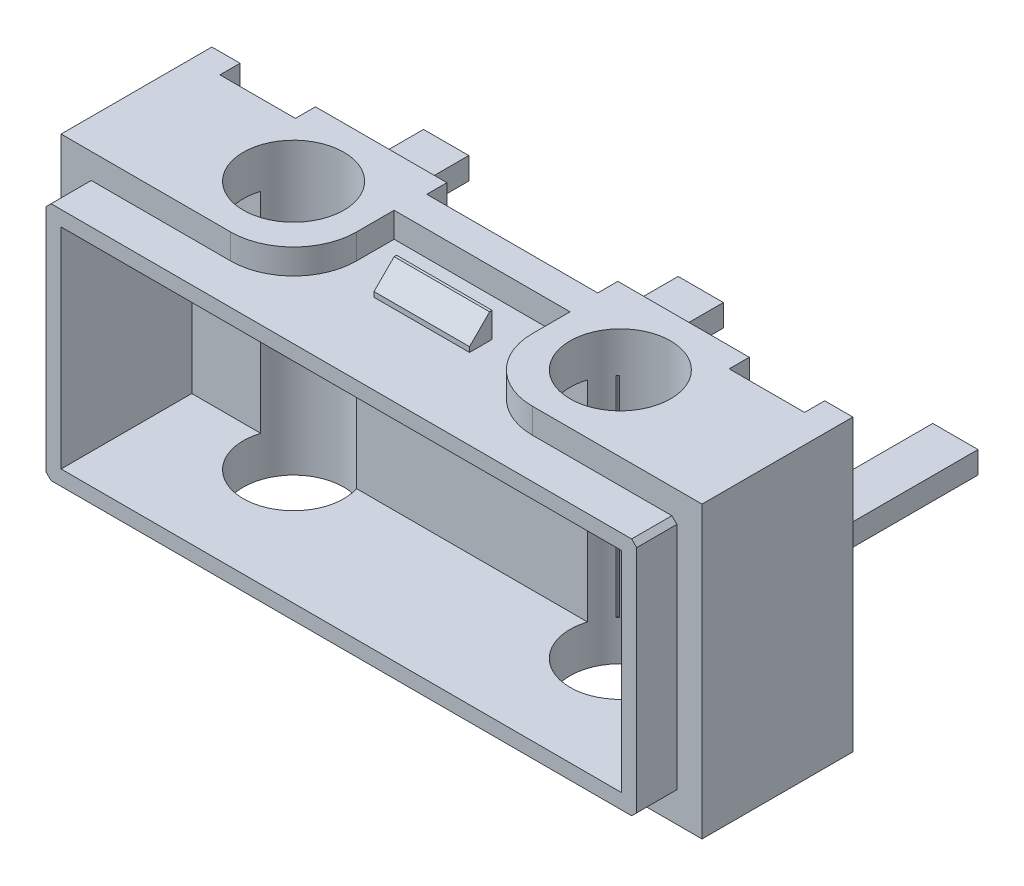
SolidWorks part; units mm, degrees
ref_plane "Face" through (0, 0, 0) normal (0, 0, 1) x (1, 0, 0)
ref_plane "Dessus" through (0, 0, 0) normal (0, 1, 0) x (1, 0, 0)
ref_plane "Droite" through (0, 0, 0) normal (1, 0, 0) x (0, 0, -1)
sketch "Esquisse1" plane through (0, 0, 0) normal (0, 0, 1) x (1, 0, 0)
  line L0 (-6.375, 0) -> (6.375, 0) construction
  line L1 (-6.375, 2.885) -> (6.375, 2.885)
  line L2 (-6.375, 2.885) -> (-6.375, -2.885)
  line L3 (-6.375, -2.885) -> (6.375, -2.885)
  line L4 (6.375, 2.885) -> (6.375, -2.885)
  line L5 (0, 2.885) -> (0, -2.885) construction
  dimension "D1" = 12.75
  dimension "D2" = 5.77
extrude "Base-Extrusion" add sketch "Esquisse1" against normal blind 3
sketch "Esquisse2" plane through (0, 0, 0) normal (0, 1, 0) x (1, 0, 0)
  line L0 (0, 3) -> (0, -1) construction
  line L1 (6.375, 3) -> (-6.375, 3) construction
  line L2 (-5.815, 3) -> (-4.315, 3)
  line L3 (-5.815, 3) -> (-5.815, 2.6)
  line L4 (-5.815, 2.6) -> (-4.315, 2.6)
  line L5 (-4.315, 3) -> (-4.315, 2.6)
  line L6 (5.815, 3) -> (5.815, 2.6)
  line L7 (5.815, 3) -> (4.315, 3)
  line L8 (4.315, 3) -> (4.315, 2.6)
  line L9 (5.815, 2.6) -> (4.315, 2.6)
  line L10 (-6.375, 3) -> (-6.375, 0) construction
  line L11 (-1.7, 3) -> (1.7, 3)
  line L12 (-1.7, 3) -> (-1.7, 2.6)
  line L13 (-1.7, 2.6) -> (1.7, 2.6)
  line L14 (1.7, 3) -> (1.7, 2.6)
  dimension "D1" = 0.4
  dimension "D2" = 1.5
  dimension "D3" = 3.4
  dimension "D4" = 0.56
extrude "Enlèv. mat.-Extru.1" cut sketch "Esquisse2" against normal through all and the other way through all
shell "Coque1" thickness 0.8
sketch "Esquisse3" plane through (0, 0, -2.6) normal (0, 0, -1) x (-1, 0, 0)
  line L0 (0, 2.885) -> (0, -2.885) construction
  line L1 (1.7, 2.885) -> (-1.7, 2.885) construction
  line L2 (-4.615, 0.22) -> (-4.615, -0.22)
  line L3 (4.615, 0.22) -> (5.515, 0.22)
  line L4 (4.615, 0.22) -> (4.615, -0.22)
  line L5 (4.615, -0.22) -> (5.515, -0.22)
  line L6 (5.515, 0.22) -> (5.515, -0.22)
  line L7 (-4.615, 0.22) -> (-5.515, 0.22)
  line L8 (-5.515, 0.22) -> (-5.515, -0.22)
  line L9 (-4.615, -0.22) -> (-5.515, -0.22)
  line L10 (-1.5256, 0) -> (1.2714, 0) construction
  line L11 (-0.45, 0.22) -> (0.45, 0.22)
  line L12 (-0.45, 0.22) -> (-0.45, -0.22)
  line L13 (-0.45, -0.22) -> (0.45, -0.22)
  line L14 (0.45, 0.22) -> (0.45, -0.22)
  line L15 (5.065, 0.7447) -> (5.065, -0.9626) construction
  line L16 (4.315, -2.885) -> (4.315, 2.885) construction
  line L17 (5.815, -2.885) -> (5.815, 2.885) construction
  dimension "D1" = 0.9
  dimension "D2" = 0.44
extrude "Boss.-Extru.1" add sketch "Esquisse3" along normal blind 3.75
sketch "Esquisse4" plane through (0, 0, 0) normal (0, 0, 1) x (1, 0, 0)
  line L0 (-5.575, -2.085) -> (5.575, -2.085) construction
  line L1 (-5.575, 2.085) -> (-5.575, -2.085) construction
  line L2 (5.575, 2.085) -> (-5.575, 2.085) construction
  line L3 (5.575, -2.085) -> (5.575, 2.085) construction
  line L4 (-5.575, -2.085) -> (5.575, -2.085)
  line L5 (-5.575, 2.085) -> (-5.575, -2.085)
  line L6 (5.575, 2.085) -> (-5.575, 2.085)
  line L7 (5.575, -2.085) -> (5.575, 2.085)
  line L10 (-6.375, -2.385) -> (6.375, -2.385)
  line L11 (-5.875, -2.385) -> (5.875, -2.385)
  line L13 (5.875, -2.885) -> (5.875, 2.885)
  line L14 (5.875, -2.385) -> (5.875, 2.385)
  line L16 (6.375, 2.385) -> (-6.375, 2.385)
  line L17 (5.875, 2.385) -> (-5.875, 2.385)
  line L19 (-5.875, 2.885) -> (-5.875, -2.885)
  line L20 (-5.875, 2.385) -> (-5.875, -2.385)
  dimension "D1" = 0.5
  dimension "D2" = 0.5
  dimension "D3" = 0.5
  dimension "D4" = 0.5
extrude "Boss.-Extru.2" add sketch "Esquisse4" along normal blind 0.8
sketch "Esquisse5" plane through (0, 2.885, 0) normal (0, 1, 0) x (1, 0, 0)
  line L0 (6.375, 0) -> (-6.375, 0) construction
  line L1 (3, 0) -> (0, 0)
  line L2 (0, 0) -> (0, 2)
  line L3 (0, 2) -> (1.75, 2)
  line L5 (1.75, 2) -> (1.75, -1.4754) construction
  line L6 (1.75, 2) -> (1.75, 1.25)
  arc A1 (1.75, 1.25) -> (3, 0) centre (3, 1.25) ccw
  dimension "D1" = 1.75
  dimension "D2" = 2
  dimension "D3" = 0.75
extrude "Enlèv. mat.-Extru.2" cut sketch "Esquisse5" against normal blind 0.5
mirror "Symétrie1" about plane through (0, 0, 0) normal (1, 0, 0) of "Enlèv. mat.-Extru.2"
mirror "Symétrie2" about plane through (0, 0, 0) normal (0, 1, 0) of "Symétrie1", "Enlèv. mat.-Extru.2"
chamfer "Chanfrein1" distance 0.1 angle 45 4 edges at (5.875, -2.385, 0.4) (5.875, 2.385, 0.4) (-5.875, 2.385, 0.4) (-5.875, -2.385, 0.4)
sketch "Esquisse6" plane through (0, 2.385, 0) normal (0, 1, 0) x (-1, 0, 0)
  line L0 (0, 0) -> (0, -3.1288) construction
  line L1 (-0.95, -0.8) -> (0.95, -0.8)
  line L2 (-0.95, -0.8) -> (-0.95, -1.25)
  line L3 (-0.95, -1.25) -> (0.95, -1.25)
  line L4 (0.95, -0.8) -> (0.95, -1.25)
  line L5 (-1.75, -2) -> (1.75, -2) construction
  dimension "D1" = 1.9
  dimension "D2" = 0.45
  dimension "D3" = 0.75
extrude "Boss.-Extru.3" add sketch "Esquisse6" along normal blind 0.5
chamfer "Chanfrein2" distance 0.4 angle 45 1 edges at (0, 2.885, -0.8)
mirror "Symétrie3" about plane through (0, 0, 0) normal (0, 1, 0) of "Chanfrein2", "Boss.-Extru.3"
sketch "Esquisse7" plane through (0, 0, 0) normal (0, 1, 0) x (1, 0, 0)
  line L0 (0, 2) -> (0, -1.0391) construction
  line L1 (2.7425, 1.5) -> (4.7767, 1.5) construction
  line L2 (-2.7425, 1.5) -> (-4.7767, 1.5) construction
  line L3 (4.315, 3) -> (1.7, 3) construction
  line L4 (6.375, 0) -> (3, 0) construction
  circle A0 centre (3.25, 1.5) radius 1
  circle A1 centre (-3.25, 1.5) radius 1
  dimension "D1" = 2
  dimension "D2" = 6.5
extrude "Enlèv. mat.-Extru.3" cut sketch "Esquisse7" against normal through all and the other way through all
